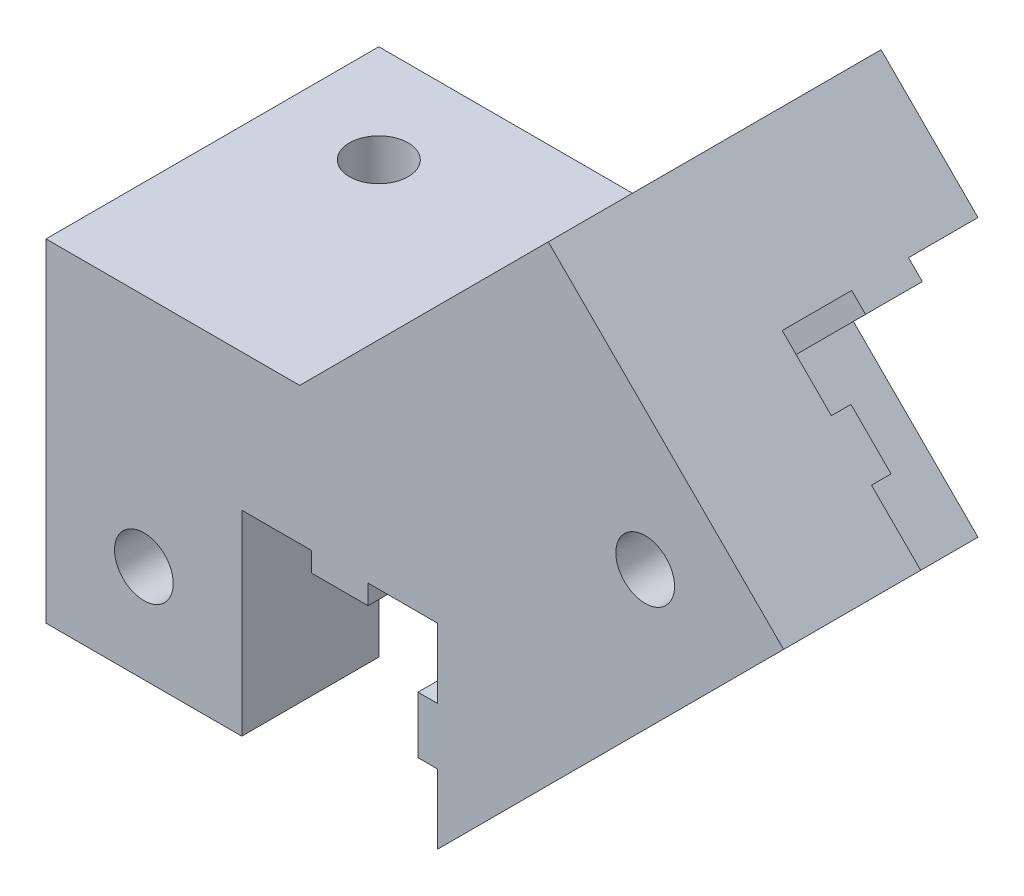
SolidWorks part; units mm, degrees
ref_plane "Front Plane" through (0, 0, 0) normal (0, 0, 1) x (1, 0, 0)
ref_plane "Top Plane" through (0, 0, 0) normal (0, 1, 0) x (1, 0, 0)
ref_plane "Right Plane" through (0, 0, 0) normal (1, 0, 0) x (0, 0, -1)
ref_plane "FrontPlane+10mm" through (0, 0, 10) normal (0, 0, 1) x (1, 0, 0)
sketch "Sketch1" plane through (0, 0, 0) normal (0, 0, 1) x (1, 0, 0)
  line L0 (-290, 0) -> (-10, 0) construction
  line L1 (0, 0) -> (-90, -90) construction
  line L2 (-10, 0) -> (0, 0) construction
  line L3 (-10, 0) -> (-10, 10) construction
  line L4 (-10, 10) -> (0, 10) construction
  line L5 (0, 0) -> (0, 10) construction
  line L6 (-90, -90) -> (-210, -90) construction
  line L7 (-300, 10) -> (-290, 10) construction
  line L8 (-300, 10) -> (-300, 0) construction
  line L9 (-90, -90) -> (-72.3223, -72.3223)
  line L10 (-290, 10) -> (-290, 0) construction
  line L11 (-210, -90) -> (-300, 0) construction
  line L12 (-88.1335, -73.9914) -> (-16.0086, -1.8665) construction
  line L13 (-110, -80) -> (-90, -80) construction
  line L14 (-110, -80) -> (-110, -90) construction
  line L15 (-90, -90) -> (-90, -80)
  line L16 (-90, -80) -> (-90, -90) construction
  line L17 (-16.0086, -1.8665) -> (-8.9376, -8.9376) construction
  line L18 (-88.1335, -73.9914) -> (-81.0624, -81.0624) construction
  line L19 (-16.0086, -1.8665) -> (0, 0) construction
  line L20 (-88.1335, -73.9914) -> (-90, -90) construction
  line L21 (-90, -80) -> (-110, -80)
  line L22 (-110, -80) -> (-110, -73)
  line L23 (-110, -73) -> (-97.0416, -73)
  line L24 (-97.0416, -73) -> (-84.3431, -60.3015)
  line L25 (-84.3431, -60.3015) -> (-72.3223, -72.3223)
  dimension "D1" = 10
  dimension "D2" = 10
  dimension "D3" = 300
  dimension "D4" = 10
  dimension "D5" = 120
  dimension "D6" = 135
  dimension "D7" = 45
  dimension "D8" = 45
  dimension "D9" = 127.2792
  dimension "D10" = 7
  dimension "D11" = 10
  dimension "D12" = 10
  dimension "D13" = 102
  dimension "D14" = 25
  dimension "D15" = 7
  dimension "D16" = 20
  dimension "D17" = 90
extrude "Main" add sketch "Sketch1" along normal blind 17
sketch "Sketch2" plane through (-72.3223, -72.3223, 0) normal (0.7071, 0.7071, 0) x (0.7071, -0.7071, 0)
  line L0 (-3.55, -10) -> (0, -10)
  line L1 (-10, -3.55) -> (-9, -3.55)
  line L2 (-9, -3.55) -> (-9, -6.45)
  line L3 (-9, -6.45) -> (-10, -6.45)
  line L4 (-6.45, -10) -> (-10, -10)
  line L5 (0, 0) -> (-17, 0) construction
  line L6 (-10, 0) -> (0, 0)
  line L7 (0, 0) -> (0, -10)
  line L8 (0, -17) -> (0, 0) construction
  line L10 (-6.45, -10) -> (-6.45, -9)
  line L11 (-6.45, -9) -> (-3.55, -9)
  line L12 (-3.55, -9) -> (-3.55, -10)
  line L13 (-10, -10) -> (-10, -6.45)
  line L15 (-10, -3.55) -> (-10, 0)
  dimension "D1" = 10
  dimension "D2" = 2.9
  dimension "D3" = 3.55
  dimension "D4" = 1
  dimension "D5" = 10
extrude "Cut-Extrude1" cut sketch "Sketch2" against normal blind 10
sketch "Sketch3" plane through (0, 0, 17) normal (0, 0, 1) x (1, 0, 0)
  line L0 (-90, -90) -> (-72.3223, -72.3223) construction
  line L1 (-72.3223, -72.3223) -> (-84.3431, -60.3015) construction
  circle A0 centre (-79.3934, -72.3223) radius 1.5
  dimension "D1" = 3
  dimension "D2" = 5
  dimension "D3" = 5
extrude "Cut-Extrude2" cut sketch "Sketch3" against normal through all
sketch "Sketch4" plane through (0, 0, 10) normal (0, 0, 1) x (1, 0, 0)
  line L0 (-96.45, -80) -> (-96.45, -81)
  line L1 (-110, -80) -> (-90, -80) construction
  line L2 (-96.45, -81) -> (-93.55, -81)
  line L3 (-93.55, -81) -> (-93.55, -80)
  line L4 (-93.55, -80) -> (-96.45, -80)
  line L6 (-90, -80) -> (-90, -90) construction
  line L7 (-90, -86.45) -> (-91, -86.45)
  line L8 (-90, -86.45) -> (-90, -83.55)
  line L9 (-90, -83.55) -> (-91, -83.55)
  line L10 (-91, -86.45) -> (-91, -83.55)
  dimension "D1" = 3.55
  dimension "D2" = 1
  dimension "D3" = 2.9
  dimension "D4" = 3.55
extrude "Boss-Extrude1" add sketch "Sketch4" along normal up to surface (7 mm away) up to face at (-77.8934, -72.3223, 17)
sketch "Sketch5" plane through (0, -80, 0) normal (0, -1, 0) x (1, 0, 0)
  line L0 (-110, 17) -> (-110, 0) construction
  line L1 (-110, 6.45) -> (-95, 6.45)
  line L2 (-110, 6.45) -> (-110, 3.55)
  line L3 (-110, 3.55) -> (-95, 3.55)
  line L4 (-95, 6.45) -> (-95, 3.55)
  line L5 (-110, 0) -> (-90, 0) construction
  dimension "D1" = 2.9
  dimension "D2" = 3.55
  dimension "D3" = 15
extrude "Boss-Extrude2" add sketch "Sketch5" along normal blind 1
sketch "Sketch6" plane through (0, -73, 0) normal (0, 1, 0) x (1, 0, 0)
  line L0 (-110, -17) -> (-110, 0) construction
  line L3 (-97.0416, 0) -> (-110, 0) construction
  circle A0 centre (-105, -5) radius 1.5
  dimension "D1" = 3
  dimension "D2" = 5
  dimension "D3" = 5
extrude "Cut-Extrude3" cut sketch "Sketch6" against normal through all
sketch "Sketch7" plane through (-110, 0, 0) normal (-1, 0, 0) x (0, 0, 1)
  line L0 (17, -80) -> (17, -90)
  line L1 (17, -90) -> (10, -90)
  line L2 (10, -90) -> (10, -86.45)
  line L3 (10, -86.45) -> (9, -86.45)
  line L4 (9, -86.45) -> (9, -83.55)
  line L5 (9, -83.55) -> (10, -83.55)
  line L6 (10, -83.55) -> (10, -80)
  line L7 (17, -80) -> (6.45, -80) construction
  line L8 (10, -80) -> (17, -80)
  line L9 (10, -79.3934) -> (10, -72.3223) construction
  dimension "D1" = 2.9
  dimension "D2" = 1
extrude "Boss-Extrude3" add sketch "Sketch7" against normal blind 10
sketch "Sketch8" plane through (0, 0, 17) normal (0, 0, 1) x (1, 0, 0)
  line L0 (-100, -90) -> (-110, -90) construction
  line L3 (-110, -73) -> (-110, -90) construction
  circle A0 centre (-105, -85) radius 1.5
  dimension "D1" = 3
  dimension "D2" = 5
  dimension "D3" = 5
extrude "Cut-Extrude4" cut sketch "Sketch8" against normal through all
sketch "Sketch9" plane through (-90, 0, 0) normal (-1, 0, 0) x (0, 0, 1)
  line L0 (0, -80) -> (0, -90) construction
  line L1 (17, -90) -> (0, -90) construction
  circle A0 centre (5, -85) radius 1.5
  dimension "D1" = 3
  dimension "D2" = 5
  dimension "D3" = 5
extrude "Cut-Extrude5" cut sketch "Sketch9" against normal through all
ref_plane "Plane2" through (0, -55, 0) normal (0, 1, 0) x (1, 0, 0)
mirror "Mirror2" [suppressed] about plane through (0, -55, 0) normal (0, 1, 0)
sketch "Sketch10" plane through (0, 0, 17) normal (0, 0, 1) x (1, 0, 0)
  line L1 (-129.0329, -56.9977) -> (-60.2872, -56.9977)
  line L2 (-129.0329, -56.9977) -> (-129.0329, -95.4249)
  line L3 (-129.0329, -95.4249) -> (-60.2872, -95.4249)
  line L4 (-60.2872, -56.9977) -> (-60.2872, -95.4249)
extrude "Cut-Extrude6" [suppressed] cut sketch "Sketch10" against normal through all
